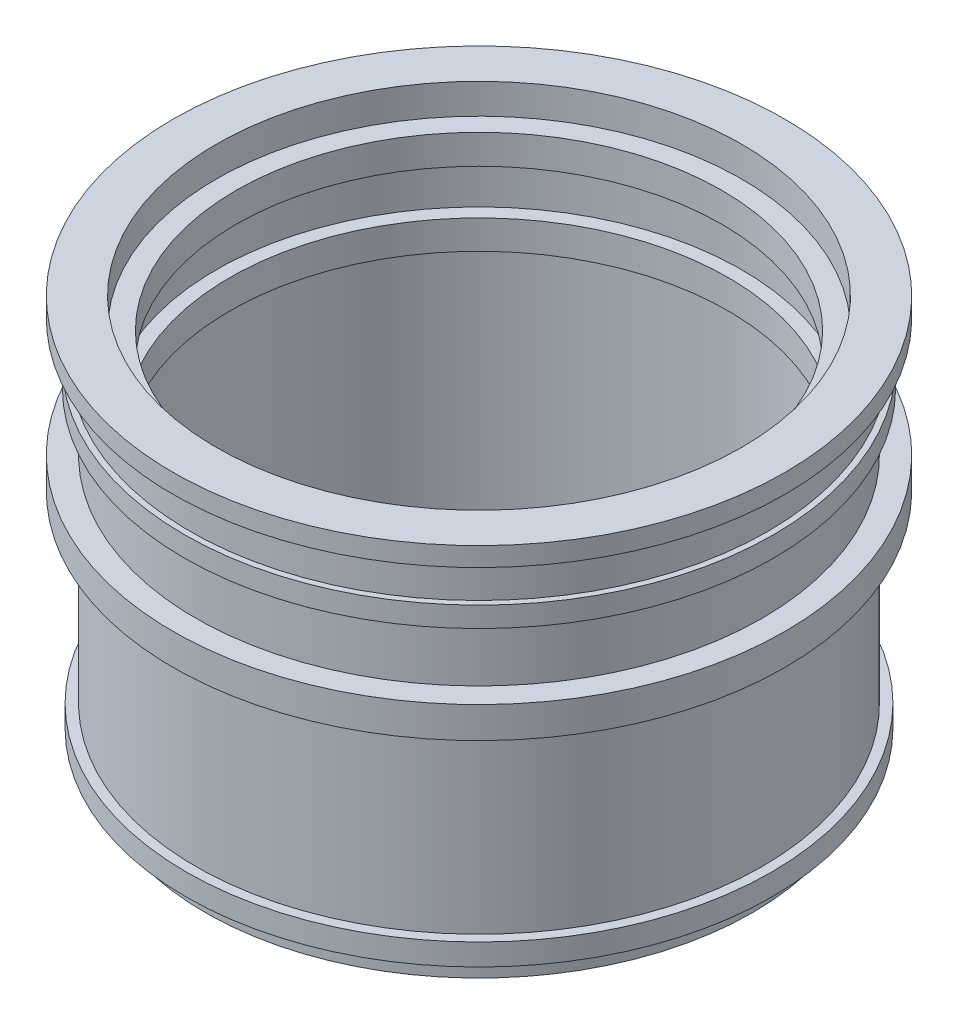
SolidWorks part; units mm, degrees
ref_plane "Front Plane" through (0, 0, 0) normal (0, 0, 1) x (1, 0, 0)
ref_plane "Top Plane" through (0, 0, 0) normal (0, 1, 0) x (1, 0, 0)
ref_plane "Right Plane" through (0, 0, 0) normal (1, 0, 0) x (0, 0, -1)
sketch "Sketch1" plane through (0, 0, 0) normal (0, 0, 1) x (1, 0, 0)
  line L0 (0, -0.3109) -> (0, 15.2358) construction
  line L1 (-75.7848, 0) -> (-75.7848, 6.3563)
  line L2 (-75.7848, 6.3563) -> (-81.0373, 6.3563)
  line L3 (-81.0373, 6.3563) -> (-81.0373, 12.3591)
  line L4 (-81.0373, 12.3591) -> (-78.411, 12.3591)
  line L5 (-78.411, 12.3591) -> (-78.411, 63.243)
  line L6 (-78.411, 63.243) -> (-84.711, 63.243)
  line L7 (-84.711, 63.243) -> (-84.711, 71.8871)
  line L8 (-84.711, 71.8871) -> (-78.411, 71.8871)
  line L9 (-78.411, 71.8871) -> (-78.411, 87.8786)
  line L10 (-78.411, 87.8786) -> (-81.561, 87.8786)
  line L11 (-81.561, 87.8786) -> (-81.561, 93.4972)
  line L12 (-81.561, 93.4972) -> (-79.986, 93.4972)
  line L13 (-79.986, 93.4972) -> (-79.986, 104.7345)
  line L14 (-79.986, 104.7345) -> (-84.711, 104.7345)
  line L15 (-84.711, 104.7345) -> (-84.711, 110)
  line L16 (-84.711, 110) -> (-72.7284, 110)
  line L17 (-72.7284, 110) -> (-72.7284, 101.6399)
  line L18 (-72.7284, 101.6399) -> (-67.2716, 101.6399)
  line L19 (-67.2716, 101.6399) -> (-67.2716, 93.4972)
  line L20 (-67.2716, 93.4972) -> (-72.7284, 93.4972)
  line L21 (-72.7284, 93.4972) -> (-72.7284, 79.8828)
  line L22 (-72.7284, 79.8828) -> (-69, 79.8828)
  line L23 (-69, 79.8828) -> (-69, 71.8871)
  line L24 (-69, 71.8871) -> (-70, 71.8871)
  line L25 (-70, 71.8871) -> (-70, 0)
  line L26 (-70, 0) -> (-75.7848, 0)
  point P26 (-79.986, 99.1158)
  dimension "D1" = 140
  dimension "D2" = 151.5696
  dimension "D3" = 162.0745
  dimension "D4" = 156.8221
  dimension "D5" = 6.3
  dimension "D6" = 1.575
  dimension "D7" = 159.9721
  dimension "D8" = 169.422
  dimension "D9" = 145.4567
  dimension "D10" = 134.5433
  dimension "D11" = 138
  dimension "D12" = 145.4567
  dimension "D13" = 7.9958
  dimension "D14" = 110
  dimension "D15" = 6.0028
  dimension "D16" = 6.3563
  dimension "D17" = 79.8828
  dimension "D18" = 63.243
  dimension "D19" = 13.6144
  dimension "D20" = 8.1427
  dimension "D21" = 32.8474
  dimension "D22" = 15.9915
  dimension "D23" = 156.8221
  dimension "D24" = 5.6186
revolve "Revolve1" add sketch "Sketch1" angle 360 about L0
